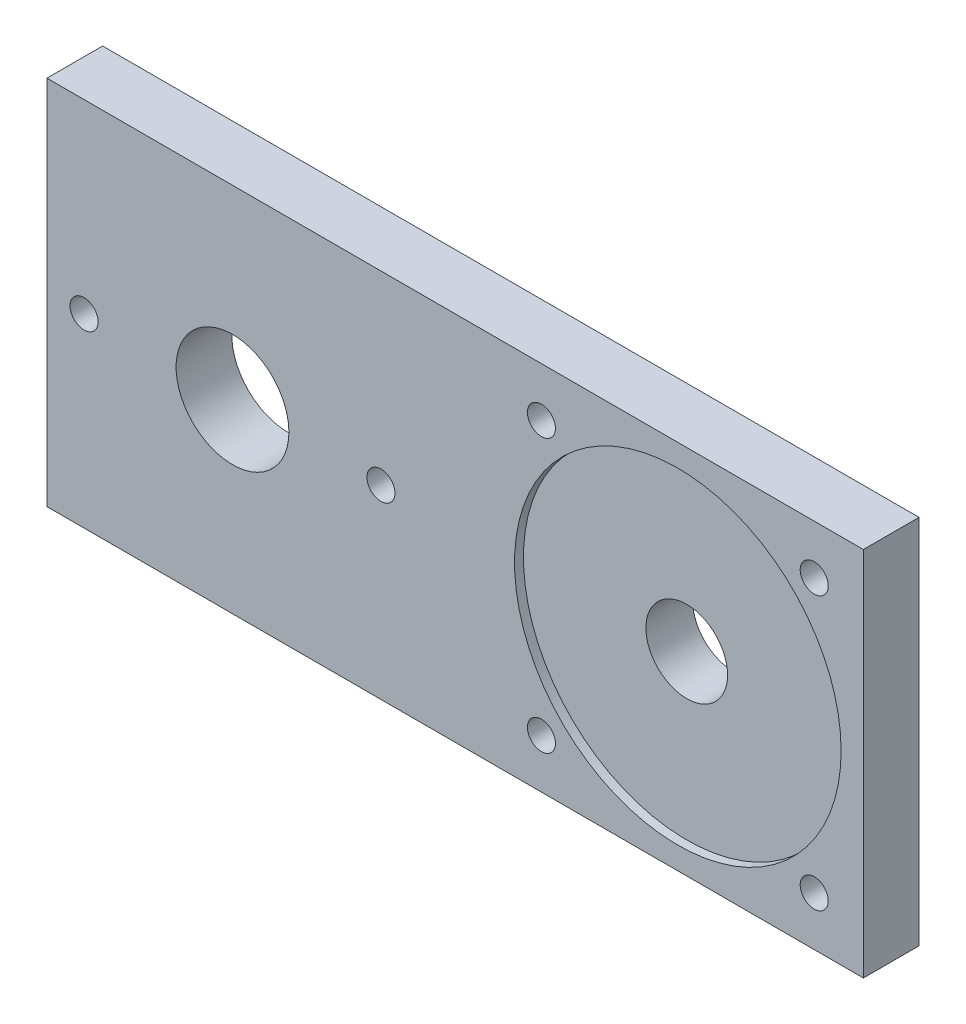
SolidWorks part; units mm, degrees
ref_plane "Front Plane" through (0, 0, 0) normal (0, 0, 1) x (1, 0, 0)
ref_plane "Top Plane" through (0, 0, 0) normal (0, 1, 0) x (1, 0, 0)
ref_plane "Right Plane" through (0, 0, 0) normal (1, 0, 0) x (0, 0, -1)
sketch "Sketch1" plane through (0, 0, 0) normal (0, 0, 1) x (1, 0, 0)
  line L1 (0, 0) -> (152.4, 0)
  line L2 (0, 0) -> (0, 76.2)
  line L3 (0, 76.2) -> (152.4, 76.2)
  line L4 (152.4, 0) -> (152.4, 76.2)
  dimension "D1" = 76.2
  dimension "D2" = 152.4
extrude "Boss-Extrude1" add sketch "Sketch1" along normal blind 9.525
sketch "Sketch2" plane through (0, 0, 9.525) normal (0, 0, 1) x (1, 0, 0)
  line L1 (0, 0) -> (152.4, 0) construction
  line L2 (38.1, 38.1) -> (114.3, 38.1) construction
  line L3 (152.4, 0) -> (152.4, 76.2) construction
  line L4 (90.9599, 14.7599) -> (137.6401, 14.7599) construction
  line L5 (90.9599, 14.7599) -> (90.9599, 61.4401) construction
  line L6 (90.9599, 61.4401) -> (137.6401, 61.4401) construction
  line L7 (137.6401, 14.7599) -> (137.6401, 61.4401) construction
  line L8 (90.9599, 14.7599) -> (137.6401, 61.4401) construction
  line L9 (90.9599, 61.4401) -> (137.6401, 14.7599) construction
  circle A0 centre (38.1, 38.1) radius 9.652
  circle A1 centre (114.3, 38.1) radius 6.985
  circle A2 centre (38.1, 38.1) radius 25.4 construction
  circle A3 centre (12.7, 38.1) radius 2.4003
  circle A4 centre (63.5, 38.1) radius 2.4003
  circle A5 centre (90.9599, 61.4401) radius 2.4003
  circle A6 centre (137.6401, 61.4401) radius 2.4003
  circle A7 centre (90.9599, 14.7599) radius 2.4003
  circle A8 centre (137.6401, 14.7599) radius 2.4003
  dimension "D1" = 19.304
  dimension "D3" = 38.1
  dimension "D4" = 50.8
  dimension "D5" = 4.8006
  dimension "D7" = 13.97
  dimension "D9" = 4.8006
  dimension "D2" = 38.1
  dimension "D6" = 76.2
  dimension "D8" = 46.6801
extrude "Cut-Extrude1" cut sketch "Sketch2" against normal blind 9.525
sketch "Sketch3" plane through (0, 0, 9.525) normal (0, 0, 1) x (1, 0, 0)
  circle A0 centre (114.3, 38.1) radius 27.94
  dimension "D1" = 55.88
extrude "Cut-Extrude2" cut sketch "Sketch3" against normal blind 1.524
sketch "Sketch4" plane through (0, 0, 0) normal (0, 0, -1) x (-1, 0, 0)
  line L5 (-146.05, 69.85) -> (-146.05, 6.35)
  line L6 (-152.4, 76.2) -> (0, 76.2)
  line L8 (-152.4, 76.2) -> (-152.4, 0)
  line L10 (-152.4, 0) -> (0, 0)
  line L12 (0, 76.2) -> (0, 0)
  line L17 (-146.05, 6.35) -> (-6.35, 6.35)
  line L18 (-6.35, 69.85) -> (-6.35, 6.35)
  line L19 (-146.05, 69.85) -> (-6.35, 69.85)
  dimension "D1" = 6.35
extrude "Cut-Extrude3" cut sketch "Sketch4" against normal through all
